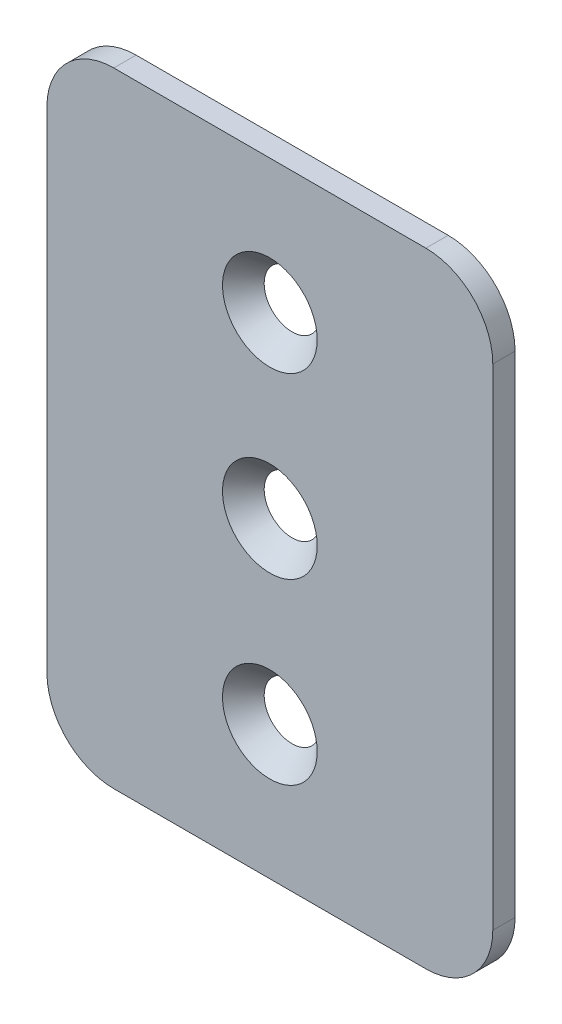
SolidWorks part; units mm, degrees
material "6061-T6 (SS)"
ref_plane "Front Plane" through (0, 0, 0) normal (0, 0, 1) x (1, 0, 0)
ref_plane "Top Plane" through (0, 0, 0) normal (0, 1, 0) x (1, 0, 0)
ref_plane "Right Plane" through (0, 0, 0) normal (1, 0, 0) x (0, 0, -1)
sketch "Sketch1" plane through (0, 0, 0) normal (0, 0, 1) x (1, 0, 0)
  line L0 (0, 25.4) -> (0, -25.4) construction
  line L2 (-22.225, 44.45) -> (22.225, 44.45)
  line L3 (-31.75, 34.925) -> (-31.75, -34.925)
  line L4 (-22.225, -44.45) -> (22.225, -44.45)
  line L5 (31.75, 34.925) -> (31.75, -34.925)
  line L6 (-31.75, 44.45) -> (31.75, -44.45) construction
  line L7 (-31.75, -44.45) -> (31.75, 44.45) construction
  circle A0 centre (0, 25.4) radius 2.5527
  circle A1 centre (0, 0) radius 2.5527
  circle A2 centre (0, -25.4) radius 2.5527
  arc A3 (22.225, 44.45) -> (31.75, 34.925) centre (22.225, 34.925) cw
  arc A4 (22.225, -44.45) -> (31.75, -34.925) centre (22.225, -34.925) ccw
  arc A5 (-31.75, -34.925) -> (-22.225, -44.45) centre (-22.225, -34.925) ccw
  arc A6 (-22.225, 44.45) -> (-31.75, 34.925) centre (-22.225, 34.925) ccw
  point P7 (0, 0)
  point P9 (0, 0)
  dimension "D4" = 5.1054
  dimension "D5" = 9.525
  dimension "D1" = 50.8
  dimension "D2" = 63.5
  dimension "D3" = 88.9
extrude "Boss-Extrude1" add sketch "Sketch1" along normal blind 3.175
hole_wizard "CSK for 1/4 Flat Head Socket Cap Screw1" positions "3DSketch1" profile "Sketch2" countersink size "1/4" standard "ANSI Inch" end condition through all
sketch3d "3DSketch1"
  line L0 (0, 25.4, 3.175) -> (0, 25.4, 0) construction
  line L1 (0, 0, 3.175) -> (0, 0, 0) construction
  line L2 (0, -25.4, 3.175) -> (0, -25.4, 0) construction
  point P0 (0, 25.4, 3.175)
  point P4 (0, 0, 3.175)
  point P8 (0, -25.4, 3.175)
sketch "Sketch2" plane through (0, 25.4, 3.175) normal (1, 0, 0) x (0, -1, 0)
  line L0 (0, 0) -> (0, 3.175)
  line L1 (0, 3.175) -> (3.3782, 3.175)
  line L2 (3.3782, 3.175) -> (3.3782, 3.8716)
  line L3 (3.3782, 3.8716) -> (6.7437, 0)
  line L5 (6.7437, 0) -> (0, 0)
  line L6 (-3.3782, 3.8716) -> (-6.7437, 0) construction
  line L11 (0, -6.35) -> (0, 107.95) construction
  dimension "Thru Hole Dia." = 6.7564
  dimension "Thru Hole Depth" = 3.175
  dimension "Near C'Sink Dia." = 13.4874
  dimension "Near C'Sink Angle" = 82
